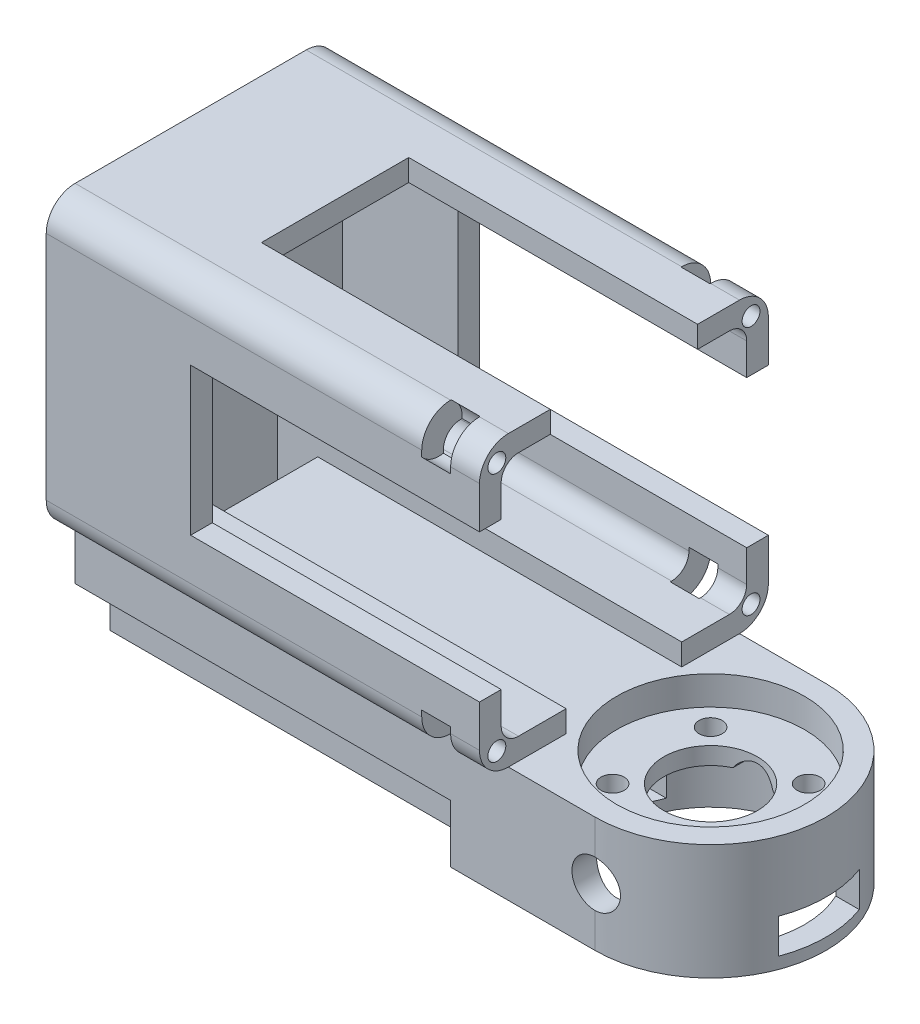
SolidWorks part; units mm, degrees
ref_plane "前视基准面" through (0, 0, 0) normal (0, 0, 1) x (1, 0, 0)
ref_plane "上视基准面" through (0, 0, 0) normal (0, 1, 0) x (1, 0, 0)
ref_plane "右视基准面" through (0, 0, 0) normal (1, 0, 0) x (0, 0, -1)
sketch "Sketch1" plane through (0, 0, 0) normal (1, 0, 0) x (0, 0, -1)
  line L1 (-25, -25) -> (25, -25)
  line L2 (-25, -25) -> (-25, 25)
  line L3 (-25, 25) -> (25, 25)
  line L4 (25, -25) -> (25, 25)
  line L5 (-25, -25) -> (25, 25) construction
  line L6 (-25, 25) -> (25, -25) construction
  point P0 (0, 0)
  dimension "D1" = 50
  dimension "D2" = 50
extrude "Boss-Extrude1" add sketch "Sketch1" against normal blind 75
fillet "Fillet1" radius 5 4 edges at (-37.5, -25, 25) (-37.5, -25, -25) (-37.5, 25, -25) (-37.5, 25, 25)
sketch "Sketch2" plane through (0, 0, 0) normal (1, 0, 0) x (0, 0, -1)
  line L1 (-21.25, -21.25) -> (21.25, -21.25)
  line L2 (-21.25, -21.25) -> (-21.25, 21.25)
  line L3 (-21.25, 21.25) -> (21.25, 21.25)
  line L4 (21.25, -21.25) -> (21.25, 21.25)
  line L5 (-21.25, -21.25) -> (21.25, 21.25) construction
  line L6 (-21.25, 21.25) -> (21.25, -21.25) construction
  point P0 (0, 0)
  dimension "D1" = 42.5
  dimension "D2" = 42.5
extrude "Cut-Extrude1" cut sketch "Sketch2" against normal blind 70
fillet "Fillet2" radius 3 4 edges at (-35, -21.25, 21.25) (-35, -21.25, -21.25) (-35, 21.25, -21.25) (-35, 21.25, 21.25)
sketch "Sketch3" plane through (0, 0, 0) normal (1, 0, 0) x (0, 0, -1)
  line L0 (20, 25) -> (-20, 25) construction
  line L1 (-12.75, 25) -> (12.75, 25)
  line L2 (-12.75, 25) -> (-12.75, 21.25)
  line L3 (-12.75, 21.25) -> (12.75, 21.25)
  line L4 (12.75, 25) -> (12.75, 21.25)
  line L5 (18.25, 21.25) -> (-18.25, 21.25) construction
  line L6 (-25, 20) -> (-25, -20) construction
  line L7 (-25, 12.75) -> (-21.25, 12.75)
  line L8 (-25, 12.75) -> (-25, -12.75)
  line L9 (-25, -12.75) -> (-21.25, -12.75)
  line L10 (-21.25, 12.75) -> (-21.25, -12.75)
  line L11 (-21.25, 18.25) -> (-21.25, -18.25) construction
  line L12 (21.25, -18.25) -> (21.25, 18.25) construction
  line L13 (21.25, 12.75) -> (25, 12.75)
  line L14 (21.25, 12.75) -> (21.25, -12.75)
  line L15 (21.25, -12.75) -> (25, -12.75)
  line L16 (25, 12.75) -> (25, -12.75)
  line L17 (25, -20) -> (25, 20) construction
  line L18 (21.25, -18.25) -> (21.25, 18.25) construction
  line L19 (18.25, 21.25) -> (-18.25, 21.25) construction
  dimension "D1" = 25.5
  dimension "D2" = 25.5
  dimension "D3" = 25.5
  dimension "D4" = 8.5
  dimension "D5" = 8.5
  dimension "D6" = 8.5
extrude "Cut-Extrude2" cut sketch "Sketch3" against normal blind 50
sketch "Sketch4" plane through (0, 0, 0) normal (1, 0, 0) x (0, 0, -1)
  line L0 (0, 0) -> (0, -25) construction
  line L1 (-20, -25) -> (20, -25) construction
  line L2 (-18.25, -21.25) -> (18.25, -21.25) construction
  line L3 (-10, -21.25) -> (10, -21.25)
  line L4 (-10, -21.25) -> (-10, -25)
  line L5 (-10, -25) -> (10, -25)
  line L6 (10, -21.25) -> (10, -25)
  dimension "D1" = 20
  dimension "D2" = 10
extrude "Cut-Extrude3" cut sketch "Sketch4" against normal blind 70
sketch "Sketch5" plane through (0, -25, 0) normal (0, -1, 0) x (1, 0, 0)
  line L1 (0, 20) -> (15, 20)
  line L2 (0, 20) -> (0, -20)
  line L3 (0, -20) -> (15, -20)
  line L4 (15, 20) -> (15, -20)
  arc A0 (15, 20) -> (15, -20) centre (15, 0) cw
  line M2 (0, 10) -> (0, 20)
  line M6 (0, -20) -> (0, -10)
  dimension "D1" = 40
  dimension "D2" = 15
extrude "Boss-Extrude2" add sketch "Sketch5" along normal blind 20 separate body contours L4 L1 L2 L3 M2 M6 | A0 L4
sketch "Sketch6" plane through (0, 0, 0) normal (-1, 0, 0) x (0, 0, 1)
  line L0 (20, -45) -> (20, -25) construction
  line L5 (-20, -25) -> (20, -25)
  line L6 (-20, -25) -> (-20, -35)
  line L7 (-20, -35) -> (20, -35)
  line L8 (20, -25) -> (20, -35)
extrude "Boss-Extrude4" add sketch "Sketch6" along normal blind 75
sketch "Sketch7" plane through (0, -25, 0) normal (0, 1, 0) x (1, 0, 0)
  line L0 (-70, 10) -> (0, 10) construction
  line L1 (-70, -10) -> (-63, -10)
  line L2 (-70, -10) -> (-70, 10)
  line L3 (-70, 10) -> (-63, 10)
  line L4 (-63, -10) -> (-63, 10)
  dimension "D1" = 7
extrude "Cut-Extrude4" cut sketch "Sketch7" against normal blind 8
sketch "Sketch8" plane through (0, 0, 0) normal (1, 0, 0) x (0, 0, -1)
  line L0 (-12.75, 25) -> (-20, 25) construction
  line L1 (-25, 20) -> (-25, 12.75) construction
  circle A0 centre (-22, 21.6) radius 1.55
  dimension "D1" = 3.1
  dimension "D2" = 3.4
  dimension "D3" = 3
extrude "Cut-Extrude5" cut sketch "Sketch8" against normal blind 5
sketch "Sketch9" plane through (-5, 0, 0) normal (1, 0, 0) x (0, 0, -1)
  circle A0 centre (-22, 21.6) radius 4
  dimension "D1" = 8
extrude "Cut-Extrude6" cut sketch "Sketch9" against normal blind 5
mirror "Mirror1" about plane through (0, 0, 0) normal (0, 1, 0) of "Cut-Extrude5", "Cut-Extrude6"
mirror "Mirror2" about plane through (0, 0, 0) normal (0, 0, 1) of "Mirror1", "Cut-Extrude5", "Cut-Extrude6"
sketch "Sketch11" plane through (0, 0, 0) normal (-1, 0, 0) x (0, 0, 1)
  line L1 (-20, -35) -> (20, -35)
  line L2 (-20, -35) -> (-20, -45)
  line L3 (-20, -45) -> (20, -45)
  line L4 (20, -35) -> (20, -45)
extrude "Boss-Extrude5" add sketch "Sketch11" along normal blind 10
sketch "Sketch12" plane through (0, 0, 20) normal (0, 0, 1) x (1, 0, 0)
  line L0 (15, -45) -> (15, -25) construction
  circle A0 centre (15, -35) radius 4
  dimension "D1" = 8
extrude "Cut-Extrude7" cut sketch "Sketch12" against normal through all
sketch "Sketch13" plane through (0, -25, 0) normal (0, 1, 0) x (1, 0, 0)
  circle A0 centre (15, 0) radius 16.25
  dimension "D1" = 32.5
extrude "Cut-Extrude8" cut sketch "Sketch13" against normal blind 5
sketch "Sketch14" plane through (0, -45, 0) normal (0, -1, 0) x (1, 0, 0)
  circle A0 centre (15, 0) radius 16.25
  dimension "D1" = 32.5
extrude "Cut-Extrude9" cut sketch "Sketch14" against normal blind 12
sketch "Sketch15" plane through (0, -30, 0) normal (0, 1, 0) x (1, 0, 0)
  circle A0 centre (15, 0) radius 8.1
  dimension "D1" = 16.2
extrude "Cut-Extrude10" cut sketch "Sketch15" against normal blind 12
sketch "Sketch16" plane through (0, -33, 0) normal (0, -1, 0) x (1, 0, 0)
  line L0 (15, 16.25) -> (15, -16.25) construction
  line L1 (-1.25, 0) -> (31.25, 0) construction
  line L2 (15, 0) -> (3.5095, 11.4905) construction
  line L3 (15, 0) -> (26.4905, 11.4905) construction
  line L4 (15, 0) -> (26.4905, -11.4905) construction
  line L5 (15, 0) -> (3.5095, -11.4905) construction
  circle A0 centre (15, 0) radius 16.25 construction
  arc A1 (11.5359, 15.8765) -> (11.5359, -15.8765) centre (15, 0) ccw construction
  arc A2 (18.4641, -15.8765) -> (18.4641, 15.8765) centre (15, 0) ccw construction
  circle A3 centre (6.5147, 8.4853) radius 2
  circle A4 centre (23.4853, 8.4853) radius 2
  circle A5 centre (23.4853, -8.4853) radius 2
  circle A6 centre (6.5147, -8.4853) radius 2
  dimension "D5" = 4
  dimension "D7" = 12
  dimension "D8" = 12
  dimension "D9" = 12
  dimension "D1" = 45
  dimension "D2" = 45
  dimension "D3" = 45
  dimension "D4" = 45
  dimension "D6" = 12
extrude "Cut-Extrude11" cut sketch "Sketch16" against normal blind 12
sketch "Sketch17" plane through (0, -33, 0) normal (0, 1, 0) x (1, 0, 0)
  line L0 (-70, -10) -> (0, -10) construction
  line L1 (-70, 10) -> (-63, 10)
  line L2 (-70, 10) -> (-70, -10)
  line L3 (-70, -10) -> (-63, -10)
  line L4 (-63, 10) -> (-63, -10)
  line L5 (-63, -10) -> (-63, 10) construction
extrude "Cut-Extrude12" cut sketch "Sketch17" against normal blind 20
sketch "Sketch18" plane through (0, -35, 0) normal (0, -1, 0) x (1, 0, 0)
  line L0 (-75, -20) -> (-75, 20) construction
  line L1 (-75, 14) -> (-10, 14)
  line L2 (-75, 14) -> (-75, -14)
  line L3 (-75, -14) -> (-10, -14)
  line L4 (-10, 14) -> (-10, -14)
  line L5 (-10, -20) -> (-10, 20) construction
  line L6 (-70, 10) -> (-63, 10) construction
  line L7 (-63, -10) -> (-70, -10) construction
  dimension "D1" = 4
  dimension "D2" = 4
extrude "Boss-Extrude6" add sketch "Sketch18" along normal blind 10
sketch "Sketch19" plane through (-75, 0, 0) normal (-1, 0, 0) x (0, 0, 1)
  line L0 (14, -45) -> (-14, -45) construction
  line L1 (-7, -43) -> (7, -43)
  line L2 (-7, -43) -> (-7, -37)
  line L3 (-7, -37) -> (7, -37)
  line L4 (7, -43) -> (7, -37)
  line L5 (-7, -43) -> (7, -37) construction
  line L6 (-7, -37) -> (7, -43) construction
  line L7 (14, -45) -> (14, -35) construction
  point P0 (0, -40)
  dimension "D1" = 6
  dimension "D2" = 14
  dimension "D3" = 2
  dimension "D4" = 7
extrude "Cut-Extrude13" cut sketch "Sketch19" against normal blind 130
sketch "Sketch20" plane through (0, -35, 0) normal (0, 1, 0) x (1, 0, 0)
  line L1 (-70, 10) -> (-63, 10)
  line L2 (-70, 10) -> (-70, -10)
  line L3 (-70, -10) -> (-63, -10)
  line L4 (-63, 10) -> (-63, -10)
extrude "Cut-Extrude14" cut sketch "Sketch20" against normal blind 3
